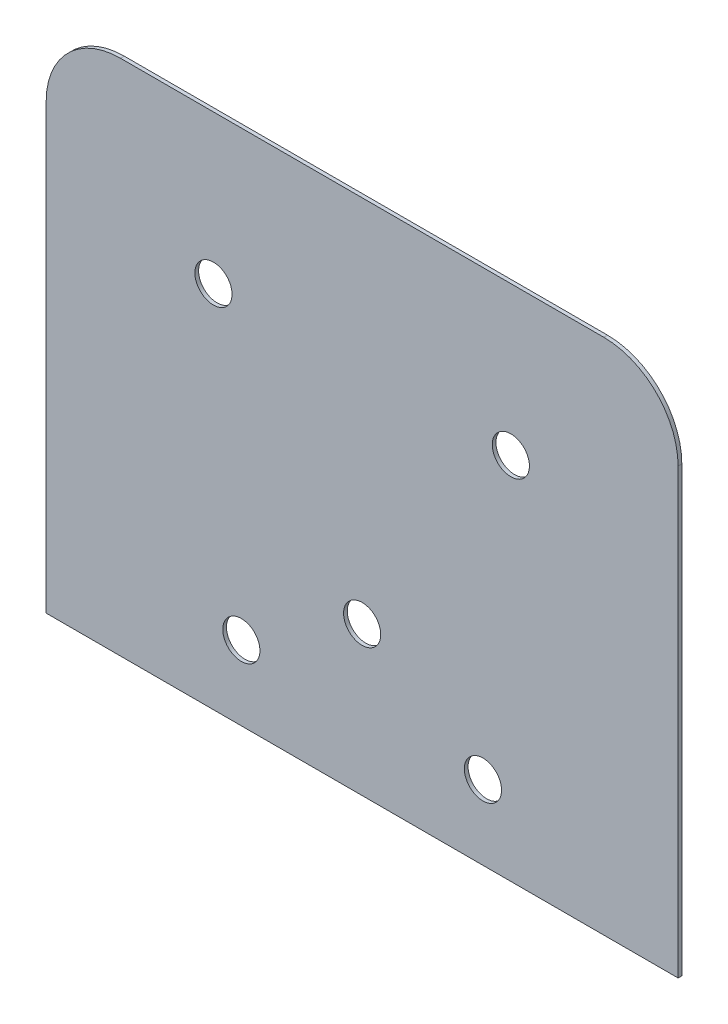
SolidWorks part; units mm, degrees
ref_plane "Plano frontal" through (0, 0, 0) normal (0, 0, 1) x (1, 0, 0)
ref_plane "Plano superior" through (0, 0, 0) normal (0, 1, 0) x (1, 0, 0)
ref_plane "Plano direito" through (0, 0, 0) normal (1, 0, 0) x (0, 0, -1)
sketch "Esboço1" plane through (0, 0, 0) normal (0, 0, 1) x (1, 0, 0)
  line L0 (-120, 318.172) -> (-152.5, 318.172)
  line L1 (-205, 178.8882) -> (-35, 178.8882)
  line L2 (-205, 178.8882) -> (-205, 298.172)
  line L3 (-185, 318.172) -> (-55, 318.172)
  line L4 (-35, 178.8882) -> (-35, 298.172)
  line L5 (-120, 318.172) -> (-87.5, 318.172)
  arc A0 (-185, 318.172) -> (-205, 298.172) centre (-185, 298.172) ccw
  arc A1 (-35, 298.172) -> (-55, 318.172) centre (-55, 298.172) ccw
  circle A2 centre (-160, 278.172) radius 5
  circle A3 centre (-80, 278.172) radius 5
  circle A4 centre (-152.5, 198.8882) radius 5
  circle A5 centre (-120, 218.8882) radius 5
  circle A6 centre (-87.5, 198.8882) radius 5
  point P18 (-79.3964, 278.172)
extrude "Ressalto-extrusão1" add sketch "Esboço1" along normal blind 1 contours L4 A1 L3 L0 A0 L2 L1 A6 A5 A4 A3 A2
